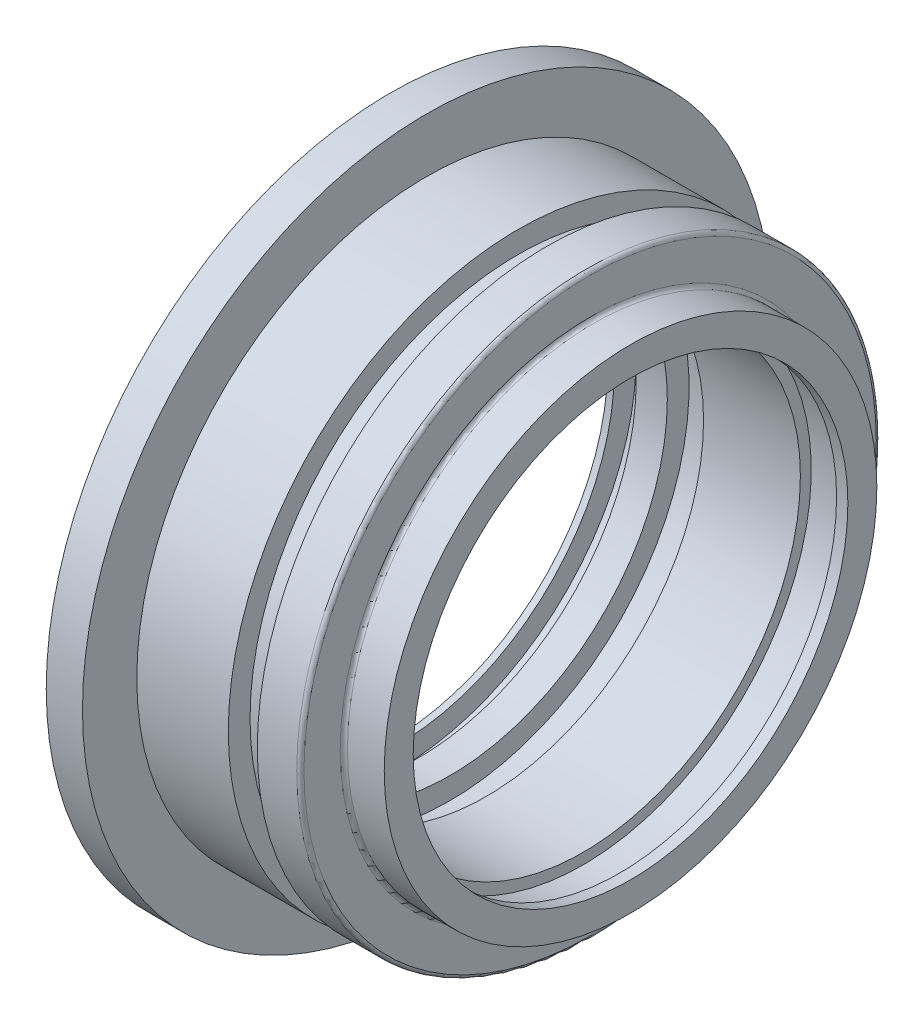
SolidWorks part; units mm, degrees
material "Alloy Steel"
ref_plane "Ön Düzlem" through (0, 0, 0) normal (0, 0, 1) x (1, 0, 0)
ref_plane "Üst Düzlem" through (0, 0, 0) normal (0, 1, 0) x (1, 0, 0)
ref_plane "Sağ Düzlem" through (0, 0, 0) normal (1, 0, 0) x (0, 0, -1)
sketch "Sketch1" plane through (0, 0, 0) normal (0, 0, 1) x (1, 0, 0)
  line L0 (-81.5782, 0) -> (83.2152, 0) construction
  line L1 (-70.6647, -47.5) -> (-65.6647, -47.5)
  line L2 (-70.6647, -47.5) -> (-70.6647, -30)
  line L3 (-70.6647, -30) -> (-69.7251, -30)
  line L4 (-69.7251, -30) -> (-69.7251, -33)
  line L5 (-69.7251, -33) -> (-66.7251, -33)
  line L6 (-66.7251, -33) -> (-66.7251, -30)
  line L7 (-66.7251, -30) -> (-62.429, -30)
  line L8 (-62.429, -30) -> (-62.429, -33)
  line L9 (-62.429, -33) -> (-57.429, -33)
  line L10 (-57.429, -33) -> (-57.429, -30)
  line L11 (-57.429, -30) -> (-44.0644, -30)
  line L12 (-44.0644, -30) -> (-44.0644, -31.5)
  line L13 (-44.0644, -31.5) -> (-39.0644, -31.5)
  line L14 (-39.0644, -31.5) -> (-39.0644, -30)
  line L15 (-39.0644, -30) -> (-37.5083, -30)
  line L16 (-37.5083, -30) -> (-37.5083, -34)
  line L17 (-37.5083, -34) -> (-42.5881, -34)
  line L18 (-43.0881, -34.5) -> (-43.0881, -39.5)
  line L19 (-43.5881, -40) -> (-49.0332, -40)
  line L20 (-65.6647, -47.5) -> (-65.6647, -40)
  line L21 (-65.6647, -40) -> (-53.0332, -40)
  line L22 (-53.0332, -40) -> (-53.0332, -37)
  line L23 (-53.0332, -37) -> (-49.0332, -37)
  line L24 (-49.0332, -37) -> (-49.0332, -40)
  arc A0 (-42.5881, -34) -> (-43.0881, -34.5) centre (-42.5881, -34.5) ccw
  arc A1 (-43.0881, -39.5) -> (-43.5881, -40) centre (-43.5881, -39.5) cw
  dimension "D4" = 40
  dimension "D1" = 47.5
  dimension "D2" = 5
  dimension "D3" = 30
  dimension "D5" = 3
  dimension "D6" = 3
  dimension "D7" = 3
  dimension "D8" = 5
  dimension "D9" = 3
  dimension "D10" = 3
  dimension "D11" = 5
  dimension "D12" = 1.5
  dimension "D13" = 1.5
  dimension "D14" = 3
  dimension "D15" = 4
  dimension "D16" = 3
revolve "Revolve1" add sketch "Sketch1" angle 360 about L0
cosmetic thread "Cosmetic Thread1" parameters "D2"=79.5
